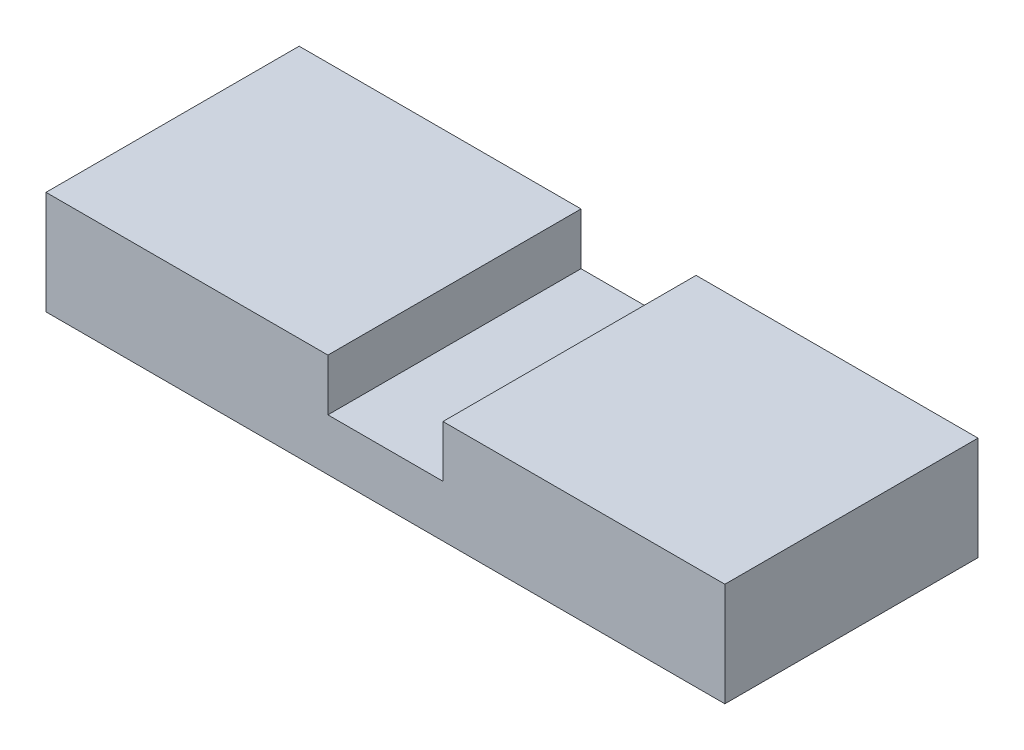
SolidWorks part; units mm, degrees
ref_plane "Front Plane" through (0, 0, 0) normal (0, 0, 1) x (1, 0, 0)
ref_plane "Top Plane" through (0, 0, 0) normal (0, 1, 0) x (1, 0, 0)
ref_plane "Right Plane" through (0, 0, 0) normal (1, 0, 0) x (0, 0, -1)
sketch "Sketch1" plane through (0, 0, 0) normal (0, 1, 0) x (1, 0, 0)
  line L1 (59, -22) -> (-59, -22)
  line L2 (59, -22) -> (59, 22)
  line L3 (59, 22) -> (-59, 22)
  line L4 (-59, -22) -> (-59, 22)
  line L5 (59, -22) -> (-59, 22) construction
  line L6 (59, 22) -> (-59, -22) construction
  point P0 (0, 0)
  dimension "D1" = 118
  dimension "D2" = 44
extrude "Extrude1" add sketch "Sketch1" along normal mid plane 18
sketch "Sketch24" plane through (0, 9, 0) normal (0, 1, 0) x (1, 0, 0)
  line L0 (59, 22) -> (-59, 22) construction
  line L1 (10, -22) -> (-10, -22)
  line L2 (10, -22) -> (10, 22)
  line L3 (10, 22) -> (-10, 22)
  line L4 (-10, -22) -> (-10, 22)
  line L5 (10, -22) -> (-10, 22) construction
  line L6 (10, 22) -> (-10, -22) construction
  point P0 (0, 0)
  dimension "D1" = 20
extrude "Extrude4" cut sketch "Sketch24" against normal blind 9
